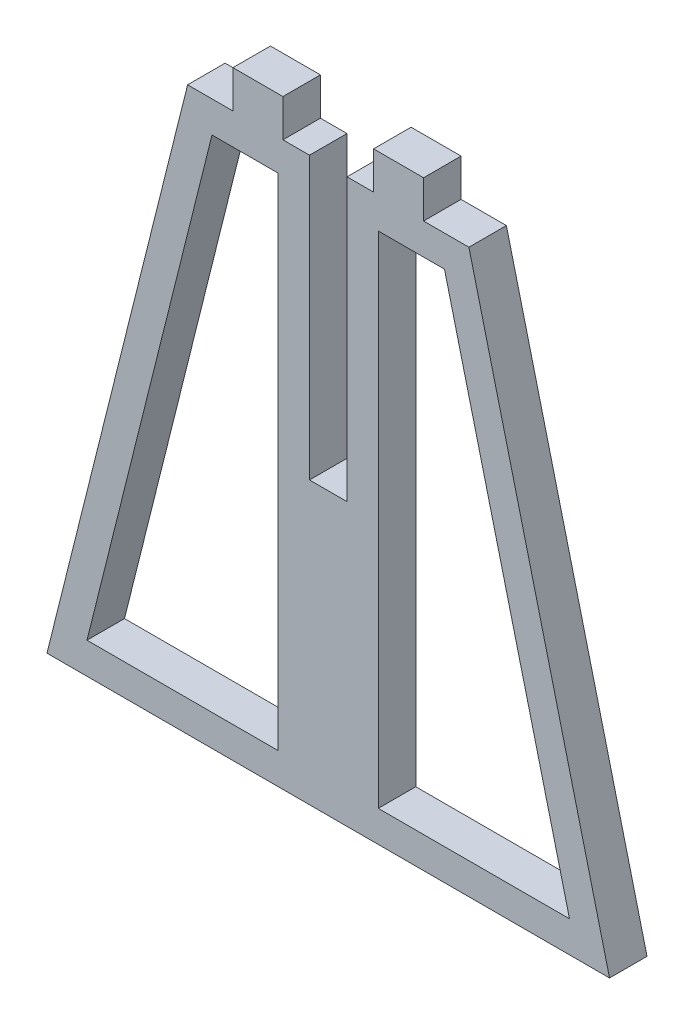
SolidWorks part; units mm, degrees
ref_plane "Front Plane" through (0, 0, 0) normal (0, 0, 1) x (1, 0, 0)
ref_plane "Top Plane" through (0, 0, 0) normal (0, 1, 0) x (1, 0, 0)
ref_plane "Right Plane" through (0, 0, 0) normal (1, 0, 0) x (0, 0, -1)
sketch "Sketch1" plane through (0, 0, 0) normal (0, 0, 1) x (1, 0, 0)
  line L0 (114.8638, 0) -> (0, 0) construction
  line L1 (0, 0) -> (-135.1751, 0) construction
  line L2 (-135.1751, 0) -> (-135.5253, -0.5253) construction
  line L3 (0, 0) -> (0, 108.3852) construction
  line L4 (0, -110.4864) -> (0, 0) construction
  line L5 (45, 15.634) -> (-45, 15.634)
  line L6 (-45, 15.634) -> (-22.5, 105.634)
  line L7 (-22.5, 105.634) -> (-15.25, 105.634)
  line L8 (22.5, 105.634) -> (45, 15.634)
  line L9 (11.25, 108.0853) -> (11.25, 102.0719) construction
  line L10 (-11.25, 108.0853) -> (-11.25, 101.1596) construction
  line L11 (-7.25, 111.634) -> (-15.25, 111.634)
  line L13 (7.25, 105.634) -> (7.25, 111.634)
  line L14 (7.25, 111.634) -> (15.25, 111.634)
  line L15 (15.25, 105.634) -> (15.25, 111.634)
  line L16 (7.25, 60.634) -> (-11.25, 60.634) construction
  line L17 (3.6524, 83.134) -> (-8.6945, 83.134) construction
  line L18 (-15.25, 105.634) -> (-15.25, 111.634)
  line L20 (-7.25, 105.634) -> (-7.25, 111.634)
  line L21 (-7.25, 105.634) -> (-3, 105.634)
  line L22 (15.25, 105.634) -> (22.5, 105.634)
  line L23 (3, 105.634) -> (7.25, 105.634)
  line L25 (-3, 105.634) -> (-3, 60.634)
  line L26 (-3, 60.634) -> (3, 60.634)
  line L27 (3, 105.634) -> (3, 60.634)
  line L28 (-8, 100.634) -> (-18.5961, 100.634)
  line L29 (-18.5961, 100.634) -> (-38.5961, 20.634)
  line L30 (-38.5961, 20.634) -> (-8, 20.634)
  line L31 (-8, 20.634) -> (-8, 100.634)
  line L32 (38.5961, 20.634) -> (8, 20.634)
  line L33 (18.5961, 100.634) -> (38.5961, 20.634)
  line L34 (8, 100.634) -> (18.5961, 100.634)
  line L35 (8, 20.634) -> (8, 100.634)
  point P15 (11.25, 105.634)
  point P28 (0, 83.134)
  dimension "D1" = 90
  dimension "D2" = 45
  dimension "D3" = 90
  dimension "D4" = 22.5
  dimension "D5" = 22.5
  dimension "D6" = 11.25
  dimension "D7" = 11.25
  dimension "D8" = 4
  dimension "D9" = 4
  dimension "D10" = 45
  dimension "D11" = 22.5
  dimension "D12" = 6
  dimension "D13" = 6
  dimension "D14" = 8
  dimension "D15" = 5
  dimension "D16" = 5
  dimension "D17" = 5
extrude "Boss-Extrude1" add sketch "Sketch1" along normal blind 6
